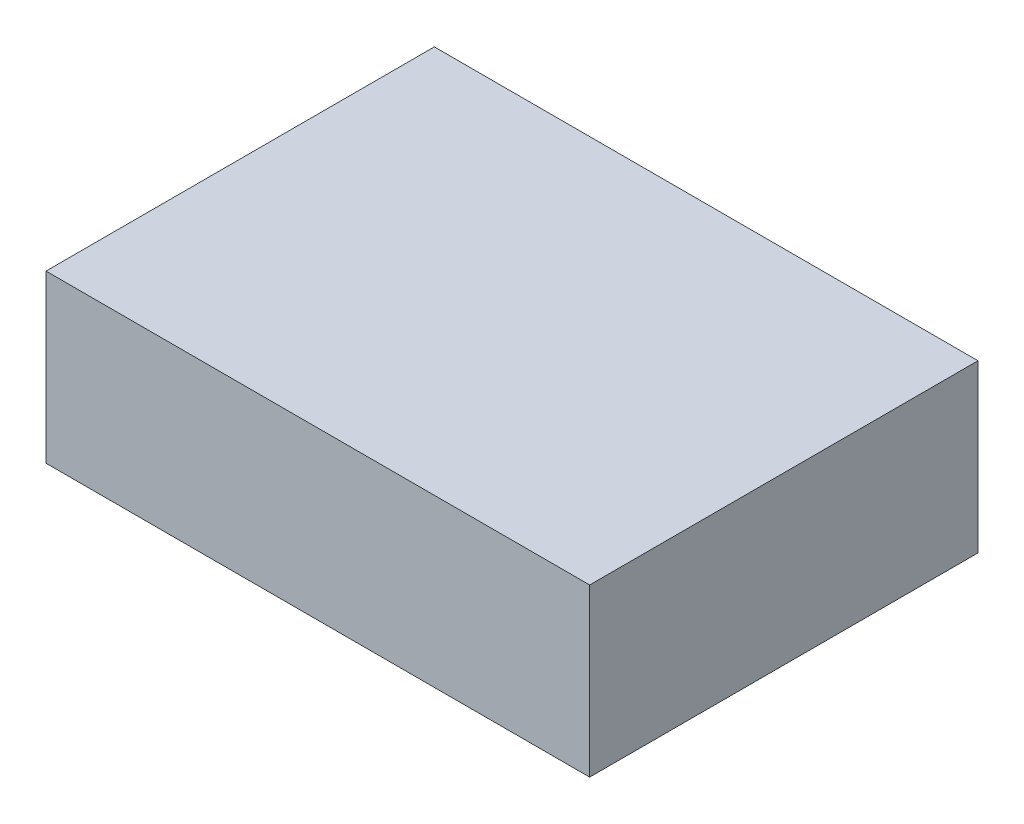
SolidWorks part; units mm, degrees
ref_plane "Front Plane" through (0, 0, 0) normal (0, 0, 1) x (1, 0, 0)
ref_plane "Top Plane" through (0, 0, 0) normal (0, 1, 0) x (1, 0, 0)
ref_plane "Right Plane" through (0, 0, 0) normal (1, 0, 0) x (0, 0, -1)
sketch "Sketch1" plane through (0, 0, 0) normal (0, 1, 0) x (1, 0, 0)
  line L1 (0, 0) -> (124.46, 0)
  line L2 (0, 0) -> (0, 88.9)
  line L3 (0, 88.9) -> (124.46, 88.9)
  line L4 (124.46, 0) -> (124.46, 88.9)
  dimension "D1" = 88.9
  dimension "D2" = 124.46
extrude "Boss-Extrude1" add sketch "Sketch1" along normal blind 38.1
